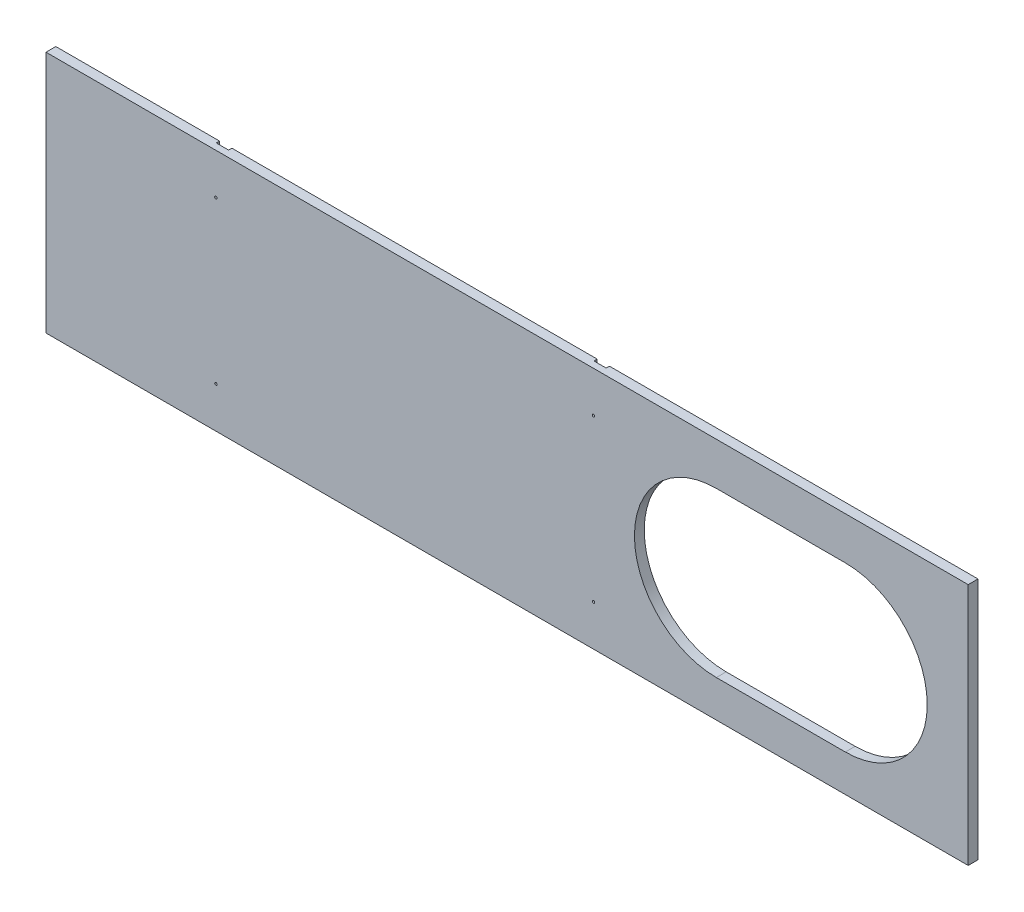
SolidWorks part; units mm, degrees
ref_plane "Plan de face" through (0, 0, 0) normal (0, 0, 1) x (1, 0, 0)
ref_plane "Plan de dessus" through (0, 0, 0) normal (0, 1, 0) x (1, 0, 0)
ref_plane "Plan de droite" through (0, 0, 0) normal (1, 0, 0) x (0, 0, -1)
sketch "Esquisse1" plane through (0, 0, 0) normal (0, 0, 1) x (1, 0, 0)
  line L0 (105.5, 148.5) -> (105.5, -148.5) construction
  line L1 (-563, -148.5) -> (563, -148.5)
  line L2 (-563, -148.5) -> (-563, 148.5)
  line L3 (-563, 148.5) -> (563, 148.5)
  line L4 (563, -148.5) -> (563, 148.5)
  line L7 (-355.5, 148.5) -> (-355.5, -148.5) construction
  line L8 (-563, -3.5) -> (563, -3.5) construction
  line L9 (255.5, 96.5) -> (413, 96.5)
  line L10 (255.5, -103.5) -> (413, -103.5)
  circle A0 centre (105.5, 98.5) radius 1.5
  circle A1 centre (105.5, -98.5) radius 1.5
  circle A2 centre (-355.5, 98.5) radius 1.5
  circle A3 centre (-355.5, -98.5) radius 1.5
  arc A4 (255.5, 96.5) -> (255.5, -103.5) centre (255.5, -3.5) ccw
  arc A5 (413, -103.5) -> (413, 96.5) centre (413, -3.5) ccw
  point P0 (0, 0)
  dimension "D9" = 50
  dimension "D10" = 50
  dimension "D14" = 200
  dimension "D15" = 200
  dimension "D16" = 150
  dimension "D17" = 150
  dimension "D1" = 1126
  dimension "D2" = 297
  dimension "D3" = 457.5
  dimension "D4" = 207.5
  dimension "D7" = 50
  dimension "D8" = 50
  dimension "D13" = 145
extrude "Boss.-Extru.1" add sketch "Esquisse1" along normal blind 12
sketch "Esquisse2" plane through (0, 0, 0) normal (0, 0, -1) x (-1, 0, 0)
  line L1 (-113, 437.7799) -> (-98, 437.7799)
  line L2 (-113, 437.7799) -> (-113, -240.7799)
  line L3 (-113, -240.7799) -> (-98, -240.7799)
  line L4 (-98, 437.7799) -> (-98, -240.7799)
  line L5 (-113, 437.7799) -> (-98, -240.7799) construction
  line L6 (-113, -240.7799) -> (-98, 437.7799) construction
  line L7 (348, 426.8405) -> (363, 426.8405)
  line L8 (348, 426.8405) -> (348, -229.8405)
  line L9 (348, -229.8405) -> (363, -229.8405)
  line L10 (363, 426.8405) -> (363, -229.8405)
  line L11 (348, 426.8405) -> (363, -229.8405) construction
  line L12 (348, -229.8405) -> (363, 426.8405) construction
  point P0 (-105.5, 98.5)
  point P6 (355.5, 98.5)
  dimension "D1" = 15
  dimension "D2" = 15
extrude "Enlèv. mat.-Extru.1" cut sketch "Esquisse2" against normal blind 4
